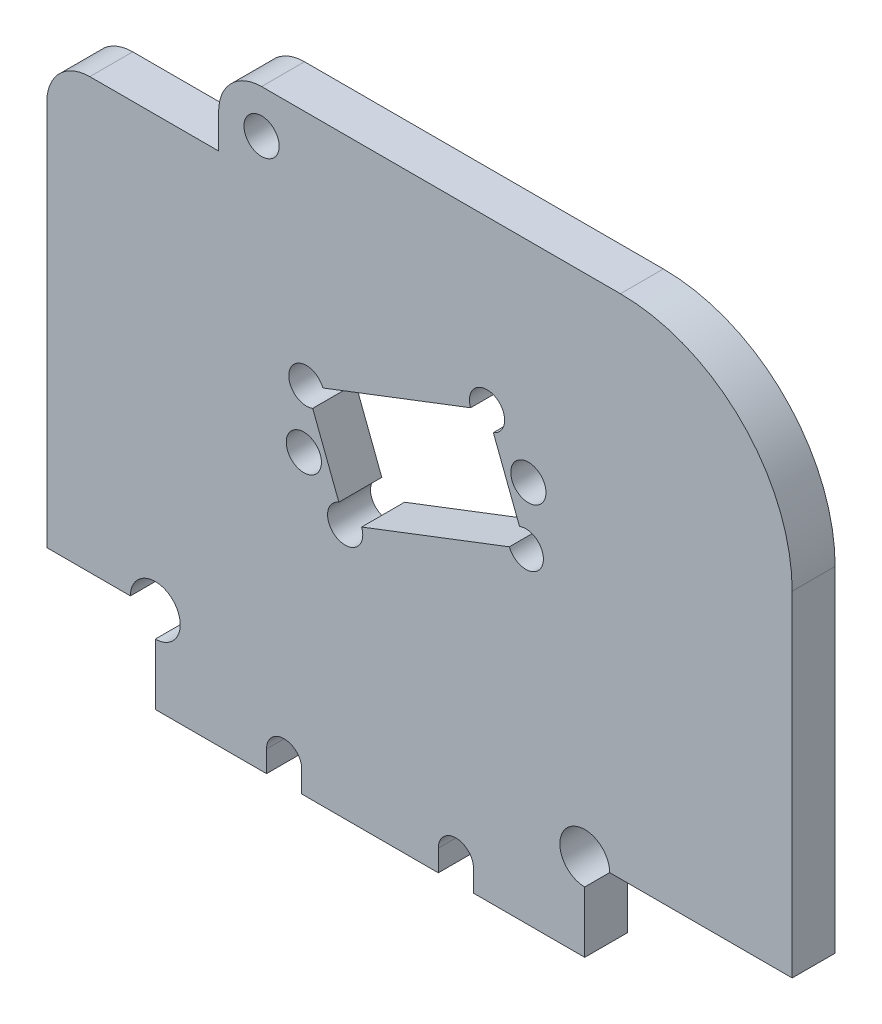
SolidWorks part; units mm, degrees
material "Acrílico (Impacto medio-alto)"
ref_plane "Piano frontale" through (0, 0, 0) normal (0, 0, 1) x (1, 0, 0)
ref_plane "Piano superiore" through (0, 0, 0) normal (0, 1, 0) x (1, 0, 0)
ref_plane "Piano destro" through (0, 0, 0) normal (1, 0, 0) x (0, 0, -1)
sketch "Schizzo1" plane through (0, 0, 0) normal (0, 0, 1) x (1, 0, 0)
  line L0 (39.1556, -41.3726) -> (-35, -41.3726)
  line L1 (0, 0) -> (0, -41.3726)
  line L2 (-35, -41.3726) -> (-35, -31.3726)
  line L3 (-27.6274, 18.6274) -> (-47.6274, 18.6274)
  line L4 (-47.6274, -31.3726) -> (-47.6274, 18.6274)
  line L5 (-35, -31.3726) -> (-47.6274, -31.3726)
  line L6 (-27.6274, 18.6274) -> (-27.6274, 22.6274)
  line L7 (-22.6274, 27.6274) -> (19.1556, 27.6274)
  line L8 (0, 0) -> (30.12, 0) construction
  line L10 (39.1556, -41.3726) -> (39.1556, 7.6274)
  line L11 (-22.6274, 22.6274) -> (0, 0) construction
  circle A0 centre (0, 0) radius 2.5
  arc A1 (19.1556, 27.6274) -> (39.1556, 7.6274) centre (19.1556, 7.6274) cw
  circle A2 centre (-20, -38.8726) radius 2.05
  circle A3 centre (0, -38.8726) radius 2.05
  arc A6 (-27.6274, 22.6274) -> (-22.6274, 27.6274) centre (-22.6274, 22.6274) cw
  circle A7 centre (-22.6274, 22.6274) radius 2.05
  dimension "D1" = 5
  dimension "D5" = 20
  dimension "D7" = 4.1
  dimension "D12" = 20
  dimension "D14" = 5
  dimension "D15" = 4.1
  dimension "D2" = 4
  dimension "D3" = 20
  dimension "D4" = 19.1556
  dimension "D8" = 15
  dimension "D9" = 2.5
  dimension "D10" = 10
  dimension "D13" = 50
  dimension "D16" = 135
  dimension "D17" = 32
extrude "Estrusione-Estrusione1" add sketch "Schizzo1" along normal blind 5
sketch "Schizzo2" plane through (0, 0, 5) normal (0, 0, 1) x (1, 0, 0)
  line L0 (5.8812, 2.2576) -> (0, 0) construction
  line L1 (-22.6274, 27.6274) -> (19.1556, 27.6274) construction
  line L2 (-15.1524, -5.8165) -> (-17.7076, -6.7973) construction
  line L3 (-12.8947, -11.698) -> (8.1389, -3.624)
  line L4 (-12.8947, -11.698) -> (-17.4101, 0.0651)
  line L5 (-17.4101, 0.0651) -> (3.6235, 8.1391)
  line L6 (8.1389, -3.624) -> (3.6235, 8.1391)
  line L7 (5.8812, 2.2576) -> (8.4359, 3.2382) construction
  circle A0 centre (-17.7076, -6.7973) radius 2.05
  circle A1 centre (8.4359, 3.2382) radius 2.05
  dimension "D7" = 4.1
  dimension "D1" = 21
  dimension "D2" = 16.2304
  dimension "D3" = 12.6
  dimension "D4" = 22.53
  dimension "D5" = 2.737
  dimension "D6" = 9.0361
extrude "Taglio-Estrusione1" cut sketch "Schizzo2" against normal through all
sketch "Croquis1" plane through (0, 0, 0) normal (0, 0, -1) x (-1, 0, 0)
  line L0 (-39.1556, -41.3726) -> (-39.1556, 7.6274) construction
  line L1 (-15, -50) -> (-39.1556, -50)
  line L2 (-15, -50) -> (-15, -31.3726)
  line L3 (-15, -31.3726) -> (-39.1556, -31.3726)
  line L4 (-39.1556, -50) -> (-39.1556, -31.3726)
  line L5 (35, -41.3726) -> (35, -31.3726) construction
  line L6 (35, -31.3726) -> (47.6274, -31.3726) construction
  dimension "D1" = 50
extrude "Cortar-Extruir1" cut sketch "Croquis1" against normal blind 10
fillet "Fillet1" radius 5 1 edges at (-47.6274, 18.6274, 2.5)
sketch "Sketch1" plane through (0, 0, 5) normal (0, 0, 1) x (1, 0, 0)
  line L0 (-20, -38.8726) -> (-20, -41.3726) construction
  line L1 (-17.95, -38.8726) -> (-17.95, -41.3726)
  line L2 (-22.05, -38.8726) -> (-22.05, -41.3726)
  line L3 (0, -38.8726) -> (0, -41.3726) construction
  line L4 (2.05, -38.8726) -> (2.05, -41.3726)
  line L5 (-2.05, -38.8726) -> (-2.05, -41.3726)
  line L6 (15, -41.3726) -> (-35, -41.3726) construction
  circle A3 centre (-35, -31.3726) radius 2.8991
  circle A4 centre (15, -31.3726) radius 2.8991
  circle A5 centre (-20, -38.8726) radius 2.05 construction
  circle A6 centre (-20, -38.8726) radius 2.05 construction
  circle A7 centre (0, -38.8726) radius 2.05 construction
  circle A8 centre (0, -38.8726) radius 2.05 construction
  arc A9 (-17.95, -38.8726) -> (-22.05, -38.8726) centre (-20, -38.8726) ccw
  arc A10 (-22.05, -41.3726) -> (-17.95, -41.3726) centre (-20, -41.3726) ccw
  arc A11 (2.05, -38.8726) -> (-2.05, -38.8726) centre (0, -38.8726) ccw
  arc A12 (-2.05, -41.3726) -> (2.05, -41.3726) centre (0, -41.3726) ccw
  point P6 (-37.8991, -31.3726)
  point P7 (-35, -34.2717)
  point P17 (-20, -40.1226)
  point P23 (0, -40.1226)
  dimension "D1" = 4.1
extrude "Cut-Extrude1" cut sketch "Sketch1" against normal up to next
sketch "Sketch2" plane through (0, 0, 5) normal (0, 0, 1) x (1, 0, 0)
  circle A0 centre (-12.8947, -11.698) radius 2.05
  circle A1 centre (8.1389, -3.624) radius 2.05
  circle A2 centre (3.6235, 8.1391) radius 2.05
  circle A3 centre (-17.4101, 0.0651) radius 2.05
  dimension "D1" = 4.1
extrude "Cut-Extrude2" cut sketch "Sketch2" against normal up to next
